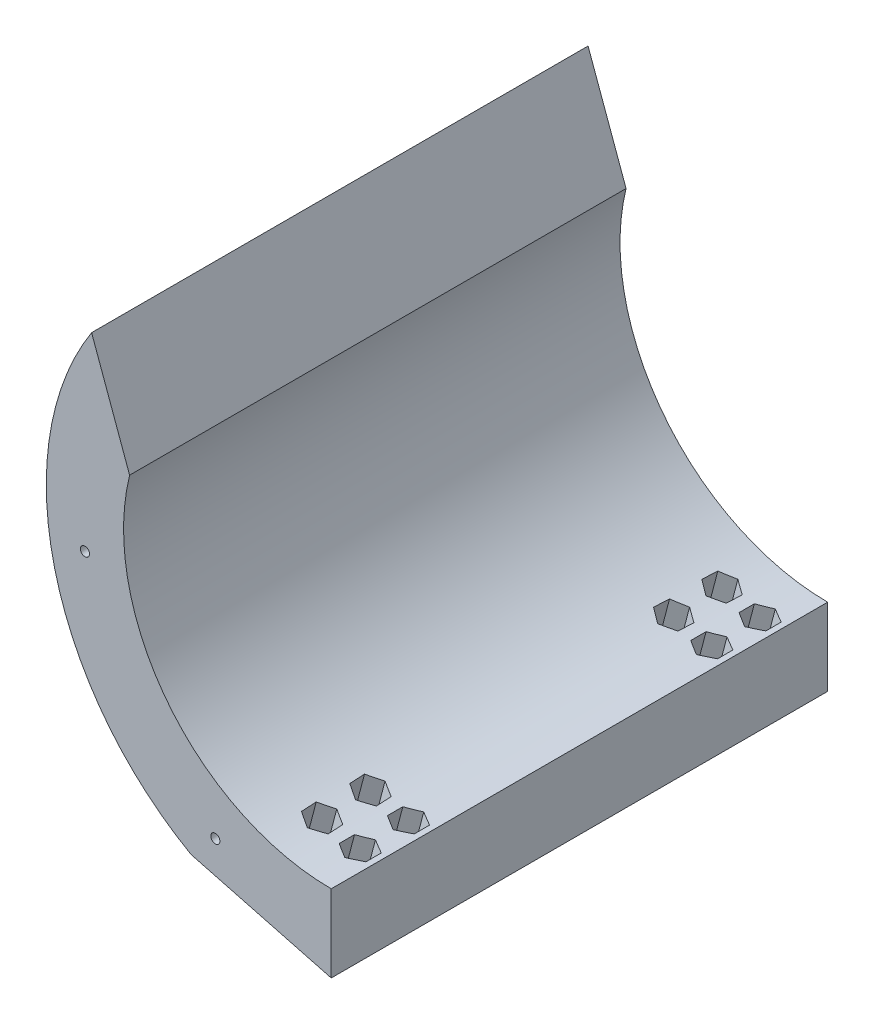
SolidWorks part; units mm, degrees
ref_plane "Front Plane" through (0, 0, 0) normal (0, 0, 1) x (1, 0, 0)
ref_plane "Top Plane" through (0, 0, 0) normal (0, 1, 0) x (1, 0, 0)
ref_plane "Right Plane" through (0, 0, 0) normal (1, 0, 0) x (0, 0, -1)
sketch "Sketch1" plane through (0, 0, 0) normal (0, 0, 1) x (1, 0, 0)
  line L0 (0, 59) -> (0, 43)
  line L1 (0, -43) -> (0, -59)
  arc A0 (0, 43) -> (0, -43) centre (0, 0) ccw
  arc A1 (0, 59) -> (0, -59) centre (0, 0) ccw
  dimension "D1" = 86
  dimension "D2" = 118
extrude "Boss-Extrude1" add sketch "Sketch1" along normal blind 102.8
sketch "Sketch3" plane through (0, 0, 102.8) normal (0, 0, 1) x (1, 0, 0)
  line L3 (0, 0) -> (0, 90)
  line L4 (0, 90) -> (-70.7573, 90)
  line L5 (-70.7573, 90) -> (-38, 0)
  line L6 (-38, 0) -> (0, 0)
  dimension "D1" = 90
  dimension "D2" = 38
  dimension "D3" = 110
extrude "Cut-Extrude1" cut sketch "Sketch3" against normal through all
sketch "Sketch4" plane through (0, 0, 102.8) normal (0, 0, 1) x (1, 0, 0)
  line L0 (0, -59) -> (-29.0143, -51.3729)
  line L1 (-29.0143, -51.3729) -> (-31.0192, -59)
  line L2 (-31.0192, -59) -> (0, -59)
  arc A0 (-49.6186, 31.9217) -> (0, -59) centre (0, 0) ccw construction
  dimension "D1" = 30
extrude "Cut-Extrude2" cut sketch "Sketch4" against normal through all
sketch "Sketch5" plane through (-14.5071, -55.1864, 0) normal (-0.2542, -0.9671, 0) x (0.9671, -0.2542, 0)
  line L0 (15, 51.4) -> (-15, 51.4) construction
  line L1 (15, 102.8) -> (15, 0) construction
  line L2 (-15, 0) -> (-15, 102.8) construction
  line L4 (15, 15) -> (4, 15) construction
  line L5 (15, 0) -> (-15, 0) construction
  circle A4 centre (-1, 20) radius 1.65
  circle A5 centre (-1, 10) radius 1.65
  circle A6 centre (-1, 92.8) radius 1.65
  circle A7 centre (-1, 82.8) radius 1.65
  circle A8 centre (7, 20) radius 1.65
  circle A9 centre (7, 10) radius 1.65
  circle A10 centre (7, 92.8) radius 1.65
  circle A11 centre (7, 82.8) radius 1.65
  dimension "D1" = 15
  dimension "D3" = 3.3
  dimension "D4" = 3.3
  dimension "D8" = 3.3
  dimension "D9" = 3.3
  dimension "D2" = 16
  dimension "D5" = 16
  dimension "D6" = 5
  dimension "D7" = 5
  dimension "D10" = 8
  dimension "D11" = 8
extrude "Cut-Extrude3" cut sketch "Sketch5" against normal up to next
sketch "Sketch6" plane through (-14.5071, -55.1864, 0) normal (-0.2542, -0.9671, 0) x (0.9671, -0.2542, 0)
  line L13 (7, 95.9726) -> (4.2525, 94.3863)
  line L14 (4.2525, 94.3863) -> (4.2525, 91.2137)
  line L27 (1.6805, 91.0976) -> (1.8146, 94.2702)
  line L28 (1.8146, 94.2702) -> (-0.866, 95.9726)
  line L29 (-0.866, 95.9726) -> (-3.6805, 94.5024)
  line L30 (-3.6805, 94.5024) -> (-3.8146, 91.3298)
  line L31 (-3.8146, 91.3298) -> (-1.134, 89.6274)
  line L32 (-1.134, 89.6274) -> (1.6805, 91.0976)
  line L33 (1.6805, 81.0976) -> (1.8146, 84.2702)
  line L34 (1.8146, 84.2702) -> (-0.866, 85.9726)
  line L35 (-0.866, 85.9726) -> (-3.6805, 84.5024)
  line L36 (-3.6805, 84.5024) -> (-3.8146, 81.3298)
  line L37 (-3.8146, 81.3298) -> (-1.134, 79.6274)
  line L38 (-1.134, 79.6274) -> (1.6805, 81.0976)
  line L39 (1.6805, 21.7024) -> (-1.134, 23.1726)
  line L40 (-1.134, 23.1726) -> (-3.8146, 21.4702)
  line L41 (-3.8146, 21.4702) -> (-3.6805, 18.2976)
  line L42 (-3.6805, 18.2976) -> (-0.866, 16.8274)
  line L43 (-0.866, 16.8274) -> (1.8146, 18.5298)
  line L44 (1.8146, 18.5298) -> (1.6805, 21.7024)
  line L45 (1.6805, 11.7024) -> (-1.134, 13.1726)
  line L46 (-1.134, 13.1726) -> (-3.8146, 11.4702)
  line L47 (-3.8146, 11.4702) -> (-3.6805, 8.2976)
  line L48 (-3.6805, 8.2976) -> (-0.866, 6.8274)
  line L49 (-0.866, 6.8274) -> (1.8146, 8.5298)
  line L50 (1.8146, 8.5298) -> (1.6805, 11.7024)
  line L51 (4.2525, 91.2137) -> (7, 89.6274)
  line L52 (7, 89.6274) -> (9.7475, 91.2137)
  line L53 (9.7475, 91.2137) -> (9.7475, 94.3863)
  line L54 (9.7475, 94.3863) -> (7, 95.9726)
  line L55 (7, 85.9726) -> (4.2525, 84.3863)
  line L56 (4.2525, 84.3863) -> (4.2525, 81.2137)
  line L57 (4.2525, 81.2137) -> (7, 79.6274)
  line L58 (7, 79.6274) -> (9.7475, 81.2137)
  line L59 (9.7475, 81.2137) -> (9.7475, 84.3863)
  line L60 (9.7475, 84.3863) -> (7, 85.9726)
  line L61 (7, 23.1726) -> (4.2525, 21.5863)
  line L62 (4.2525, 21.5863) -> (4.2525, 18.4137)
  line L63 (4.2525, 18.4137) -> (7, 16.8274)
  line L64 (7, 16.8274) -> (9.7475, 18.4137)
  line L65 (9.7475, 18.4137) -> (9.7475, 21.5863)
  line L66 (9.7475, 21.5863) -> (7, 23.1726)
  line L67 (7, 13.1726) -> (4.2525, 11.5863)
  line L68 (4.2525, 11.5863) -> (4.2525, 8.4137)
  line L69 (4.2525, 8.4137) -> (7, 6.8274)
  line L70 (7, 6.8274) -> (9.7475, 8.4137)
  line L71 (9.7475, 8.4137) -> (9.7475, 11.5863)
  line L72 (9.7475, 11.5863) -> (7, 13.1726)
  circle A0 centre (-1, 92.8) radius 2.75 construction
  circle A1 centre (-1, 82.8) radius 2.75 construction
  circle A4 centre (-1, 20) radius 2.75 construction
  circle A5 centre (-1, 10) radius 2.75 construction
  circle A6 centre (7, 92.8) radius 2.7475 construction
  circle A7 centre (7, 82.8) radius 2.7475 construction
  circle A8 centre (7, 20) radius 2.7475 construction
  circle A9 centre (7, 10) radius 2.7475 construction
  dimension "D1" = 5.5
  dimension "D2" = 5.5
  dimension "D3" = 5.5
  dimension "D4" = 5.5
extrude "Cut-Extrude4" cut sketch "Sketch6" against normal through all from offset 5 offset against normal yes
sketch "Sketch7" plane through (0, 0, 0) normal (0, 0, -1) x (-1, 0, 0)
  line L0 (0, -59) -> (0, -43) construction
  circle A0 centre (24, -46) radius 0.95
  circle A1 centre (51, -8) radius 0.95
  dimension "D1" = 1.9
  dimension "D2" = 1.9
  dimension "D3" = 24
  dimension "D4" = 13
  dimension "D5" = 51
  dimension "D6" = 51
extrude "Cut-Extrude5" cut sketch "Sketch7" against normal through all
